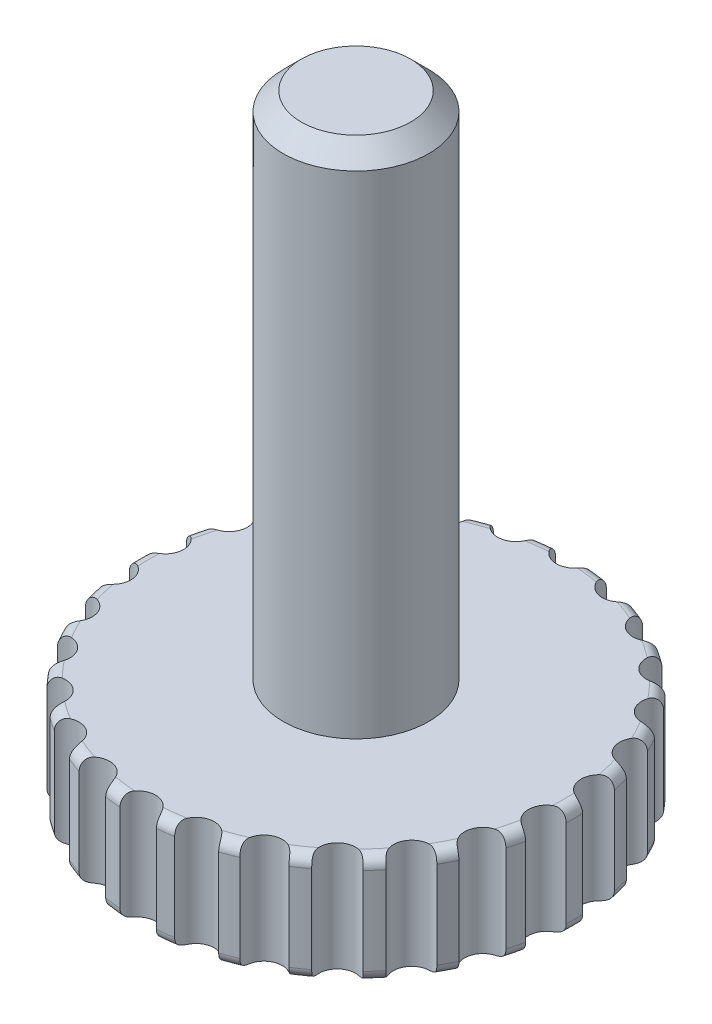
SolidWorks part; units mm, degrees
ref_plane "Front Plane" through (0, 0, 0) normal (0, 0, 1) x (1, 0, 0)
ref_plane "Top Plane" through (0, 0, 0) normal (0, 1, 0) x (1, 0, 0)
ref_plane "Right Plane" through (0, 0, 0) normal (1, 0, 0) x (0, 0, -1)
sketch "Sketch1" plane through (0, 0, 0) normal (0, 0, 1) x (1, 0, 0)
  line L0 (0, 25.4762) -> (0, -8.9048) construction
  line L1 (0, 17) -> (-2, 17)
  line L2 (-2, 17) -> (-2, 3)
  line L3 (-2, 3) -> (-6, 3)
  line L4 (-6, 3) -> (-6, 0)
  line L5 (-6, 0) -> (0, 0)
  line L6 (0, 17) -> (0, 0)
  dimension "D1" = 4
  dimension "D2" = 12
  dimension "D3" = 14
  dimension "D4" = 3
revolve "Revolve1" add sketch "Sketch1" angle 360 about L6
chamfer "Chamfer1" distance 0.5 angle 45 1 edges at (-2, 17, 0)
fillet "Fillet1" radius 0.3 2 edges at (-6, 3, 0) (-6, 0, 0)
sketch "Sketch2" plane through (0, 0, 0) normal (0, -1, 0) x (-1, 0, 0)
  circle A0 centre (0, -6) radius 0.5
  circle A1 centre (0, 0) radius 6 construction
  circle A2 centre (-1.4359, -5.8257) radius 0.5
  circle A3 centre (-2.7883, -5.3127) radius 0.5
  circle A4 centre (-3.9787, -4.4911) radius 0.5
  circle A5 centre (-4.9379, -3.4084) radius 0.5
  circle A6 centre (-5.6101, -2.1276) radius 0.5
  circle A7 centre (-5.9563, -0.7232) radius 0.5
  circle A8 centre (-5.9563, 0.7232) radius 0.5
  circle A9 centre (-5.6101, 2.1276) radius 0.5
  circle A10 centre (-4.9379, 3.4084) radius 0.5
  circle A11 centre (-3.9787, 4.4911) radius 0.5
  circle A12 centre (-2.7883, 5.3127) radius 0.5
  circle A13 centre (-1.4359, 5.8257) radius 0.5
  circle A14 centre (0, 6) radius 0.5
  circle A15 centre (1.4359, 5.8257) radius 0.5
  circle A16 centre (2.7883, 5.3127) radius 0.5
  circle A17 centre (3.9787, 4.4911) radius 0.5
  circle A18 centre (4.9379, 3.4084) radius 0.5
  circle A19 centre (5.6101, 2.1276) radius 0.5
  circle A20 centre (5.9563, 0.7232) radius 0.5
  circle A21 centre (5.9563, -0.7232) radius 0.5
  circle A22 centre (5.6101, -2.1276) radius 0.5
  circle A23 centre (4.9379, -3.4084) radius 0.5
  circle A24 centre (3.9787, -4.4911) radius 0.5
  circle A25 centre (2.7883, -5.3127) radius 0.5
  circle A26 centre (1.4359, -5.8257) radius 0.5
  point P56 (0, 0)
  dimension "D1" = 1
  dimension "D2" = 26
extrude "Cut-Extrude1" cut sketch "Sketch2" against normal up to next
